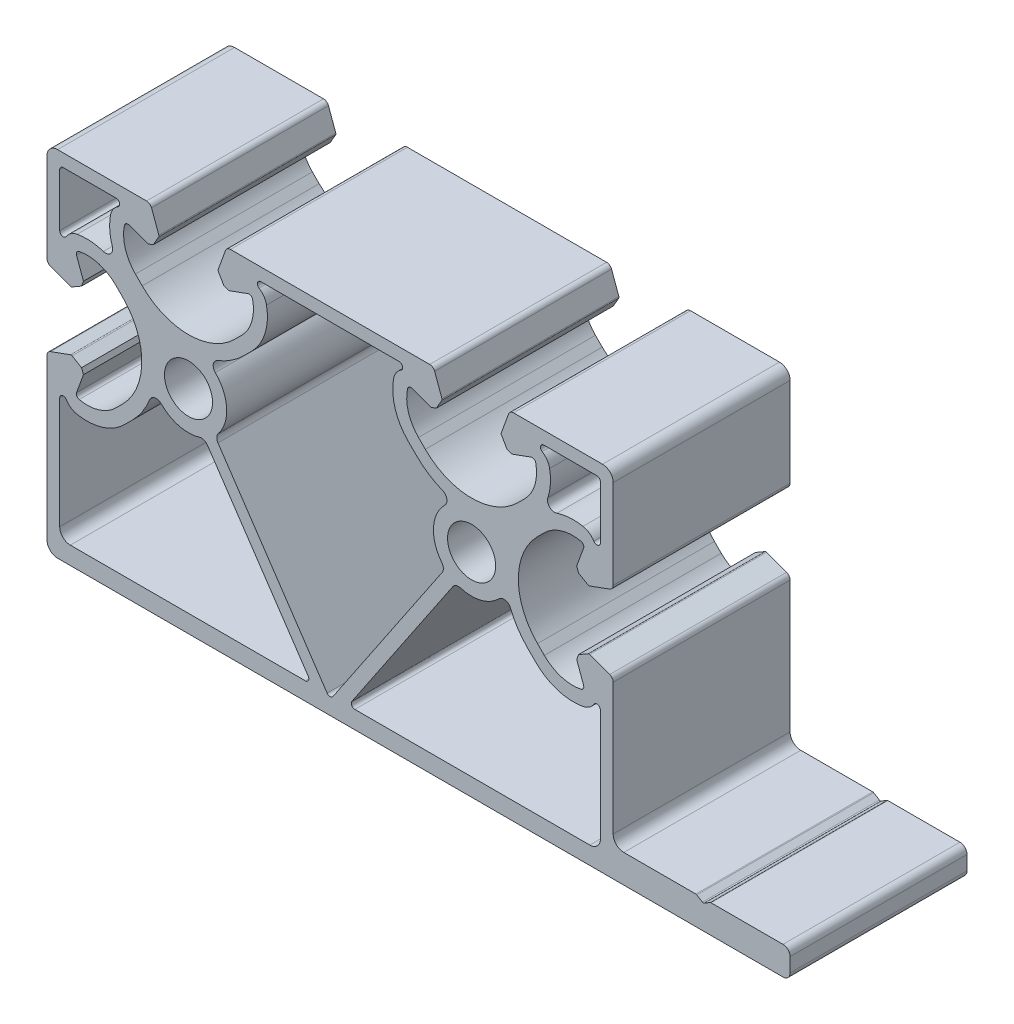
SolidWorks part; units mm, degrees
material "6005-T5"
ref_plane "Front" through (0, 0, 0) normal (0, 0, 1) x (1, 0, 0)
ref_plane "Top" through (0, 0, 0) normal (0, 1, 0) x (1, 0, 0)
ref_plane "Right" through (0, 0, 0) normal (1, 0, 0) x (0, 0, -1)
sketch "Sk Main Extrusion" plane through (0, 0, 0) normal (0, 0, 1) x (1, 0, 0)
  line L78 (-11.0507, 39.0722) -> (-12.1865, 37.9365)
  line L79 (-15.8391, 25.4341) -> (-0.4147, 2.5366)
  line L80 (0.4147, 2.5366) -> (15.8391, 25.4341)
  line L81 (12.1865, 37.9365) -> (11.0507, 39.0722)
  line L82 (9.7655, 48.2) -> (-9.7655, 48.2)
  line L83 (-27.9365, 22.1865) -> (-29.0722, 21.0507)
  line L84 (-38.2, 19.7655) -> (-38.2, 4)
  line L85 (-36.7, 2.5) -> (-3.5, 2.5)
  line L86 (-3.0853, 3.2793) -> (-17.332, 24.4285)
  line L87 (-38.2, 47.7) -> (-38.2, 40.2345)
  line L88 (-30.2345, 48.2) -> (-37.7, 48.2)
  line L89 (17.332, 24.4285) -> (3.0853, 3.2793)
  line L90 (3.5, 2.5) -> (36.7, 2.5)
  line L91 (38.2, 4) -> (38.2, 19.7655)
  line L92 (29.0722, 21.0507) -> (27.9365, 22.1865)
  line L93 (38.2, 40.2345) -> (38.2, 47.7)
  line L94 (37.7, 48.2) -> (30.2345, 48.2)
  line L95 (-36.6712, 25.8099) -> (-39.5065, 24.7779)
  line L96 (-40, 24.0732) -> (-40, 1.5)
  line L97 (-38.5, 0) -> (64, 0)
  line L98 (65, 1) -> (65, 3)
  line L99 (64, 4) -> (53.8207, 4)
  line L100 (53.6919, 3.9643) -> (52.8788, 3.4757)
  line L101 (52.6212, 3.4757) -> (51.8081, 3.9643)
  line L102 (51.6793, 4) -> (41.5, 4)
  line L103 (40, 5.5) -> (40, 24.0732)
  line L104 (39.5065, 24.7779) -> (36.6712, 25.8099)
  line L105 (36.4607, 25.7915) -> (35.1113, 25.0124)
  line L106 (35.1113, 25.0124) -> (34.8453, 24.2815)
  line L107 (34.8453, 24.2815) -> (35.8198, 21.6038)
  line L108 (30.2727, 22.4958) -> (29.3093, 23.4593)
  line L109 (29.3093, 36.5407) -> (30.2727, 37.5042)
  line L110 (35.8198, 38.3962) -> (34.8453, 35.7185)
  line L111 (34.8453, 35.7185) -> (35.1113, 34.9876)
  line L112 (35.1113, 34.9876) -> (36.4607, 34.2085)
  line L113 (36.6712, 34.1901) -> (39.5065, 35.2221)
  line L114 (40, 35.9268) -> (40, 48.5)
  line L115 (38.5, 50) -> (25.9268, 50)
  line L116 (25.2221, 49.5065) -> (24.1901, 46.6712)
  line L117 (24.2085, 46.4607) -> (24.9876, 45.1113)
  line L118 (24.9876, 45.1113) -> (25.7185, 44.8453)
  line L119 (25.7185, 44.8453) -> (28.3962, 45.8198)
  line L120 (27.5042, 40.2727) -> (26.5407, 39.3093)
  line L121 (13.4593, 39.3093) -> (12.4958, 40.2727)
  line L122 (11.6038, 45.8198) -> (14.2815, 44.8453)
  line L123 (14.2815, 44.8453) -> (15.0124, 45.1113)
  line L124 (15.0124, 45.1113) -> (15.7915, 46.4607)
  line L125 (15.8099, 46.6712) -> (14.7779, 49.5065)
  line L126 (14.0732, 50) -> (-14.0732, 50)
  line L127 (-14.7779, 49.5065) -> (-15.8099, 46.6712)
  line L128 (-15.7915, 46.4607) -> (-15.0124, 45.1113)
  line L129 (-15.0124, 45.1113) -> (-14.2815, 44.8453)
  line L130 (-14.2815, 44.8453) -> (-11.6038, 45.8198)
  line L131 (-12.4958, 40.2727) -> (-13.4593, 39.3093)
  line L132 (-26.5407, 39.3093) -> (-27.5042, 40.2727)
  line L133 (-28.3962, 45.8198) -> (-25.7185, 44.8453)
  line L134 (-25.7185, 44.8453) -> (-24.9876, 45.1113)
  line L135 (-24.9876, 45.1113) -> (-24.2085, 46.4607)
  line L136 (-24.1901, 46.6712) -> (-25.2221, 49.5065)
  line L137 (-25.9268, 50) -> (-38.5, 50)
  line L138 (-40, 48.5) -> (-40, 35.9268)
  line L139 (-39.5065, 35.2221) -> (-36.6712, 34.1901)
  line L140 (-36.4607, 34.2085) -> (-35.1113, 34.9876)
  line L141 (-35.1113, 34.9876) -> (-34.8453, 35.7185)
  line L142 (-34.8453, 35.7185) -> (-35.8198, 38.3962)
  line L143 (-30.2727, 37.5042) -> (-29.3093, 36.5407)
  line L144 (-29.3093, 23.4593) -> (-30.2727, 22.4958)
  line L145 (-35.8198, 21.6038) -> (-34.8453, 24.2815)
  line L146 (-34.8453, 24.2815) -> (-35.1113, 25.0124)
  line L147 (-35.1113, 25.0124) -> (-36.4607, 25.7915)
  circle A96 centre (-20, 30) radius 3.4
  circle A97 centre (20, 30) radius 3.4
  arc A98 (-9.7655, 48.2) -> (-10.0289, 47.275) centre (-9.7655, 47.7) ccw
  arc A99 (-8.9787, 45.7377) -> (-10.0289, 47.275) centre (-11.2405, 45.32) ccw
  arc A100 (-11.0507, 39.0722) -> (-8.9787, 45.7377) centre (-16.354, 44.3755) ccw
  arc A101 (-15.8873, 35.4939) -> (-12.1865, 37.9365) centre (-20, 45.75) ccw
  arc A102 (-15.8873, 35.4939) -> (-16.2159, 33.8523) centre (-15.5151, 34.5657) ccw
  arc A103 (-15.7895, 26.6189) -> (-16.2159, 33.8523) centre (-20, 30) ccw
  arc A104 (-15.7895, 26.6189) -> (-15.8391, 25.4341) centre (-15.0098, 25.9928) ccw
  arc A105 (-0.4147, 2.5366) -> (0.4147, 2.5366) centre (0, 2.816) ccw
  arc A106 (15.8391, 25.4341) -> (15.7895, 26.6189) centre (15.0098, 25.9928) ccw
  arc A107 (16.2159, 33.8523) -> (15.7895, 26.6189) centre (20, 30) ccw
  arc A108 (16.2159, 33.8523) -> (15.8873, 35.4939) centre (15.5151, 34.5657) ccw
  arc A109 (12.1865, 37.9365) -> (15.8873, 35.4939) centre (20, 45.75) ccw
  arc A110 (8.9787, 45.7377) -> (11.0507, 39.0722) centre (16.354, 44.3755) ccw
  arc A111 (10.0289, 47.275) -> (8.9787, 45.7377) centre (11.2405, 45.32) ccw
  arc A112 (10.0289, 47.275) -> (9.7655, 48.2) centre (9.7655, 47.7) ccw
  arc A113 (-23.8523, 26.2159) -> (-25.4939, 25.8873) centre (-24.5657, 25.5151) ccw
  arc A114 (-27.9365, 22.1865) -> (-25.4939, 25.8873) centre (-35.75, 30) ccw
  arc A115 (-39.5065, 24.7779) -> (-40, 24.0732) centre (-39.25, 24.0732) ccw
  arc A116 (-40, 1.5) -> (-38.5, 0) centre (-38.5, 1.5) ccw
  arc A117 (64, 0) -> (65, 1) centre (64, 1) ccw
  arc A118 (65, 3) -> (64, 4) centre (64, 3) ccw
  arc A119 (53.8207, 4) -> (53.6919, 3.9643) centre (53.8207, 3.75) ccw
  arc A120 (52.6212, 3.4757) -> (52.8788, 3.4757) centre (52.75, 3.69) ccw
  arc A121 (51.8081, 3.9643) -> (51.6793, 4) centre (51.6793, 3.75) ccw
  arc A122 (40, 5.5) -> (41.5, 4) centre (41.5, 5.5) ccw
  arc A123 (40, 24.0732) -> (39.5065, 24.7779) centre (39.25, 24.0732) ccw
  arc A124 (36.6712, 25.8099) -> (36.4607, 25.7915) centre (36.5857, 25.575) ccw
  arc A125 (35.4507, 20.943) -> (35.8198, 21.6038) centre (35.35, 21.4328) ccw
  arc A126 (30.2727, 22.4958) -> (35.4507, 20.943) centre (34.3032, 26.5263) ccw
  arc A127 (29.3093, 36.5407) -> (29.3093, 23.4593) centre (35.85, 30) ccw
  arc A128 (35.4507, 39.057) -> (30.2727, 37.5042) centre (34.3032, 33.4737) ccw
  arc A129 (35.8198, 38.3962) -> (35.4507, 39.057) centre (35.35, 38.5672) ccw
  arc A130 (36.4607, 34.2085) -> (36.6712, 34.1901) centre (36.5857, 34.425) ccw
  arc A131 (39.5065, 35.2221) -> (40, 35.9268) centre (39.25, 35.9268) ccw
  arc A132 (40, 48.5) -> (38.5, 50) centre (38.5, 48.5) ccw
  arc A133 (25.9268, 50) -> (25.2221, 49.5065) centre (25.9268, 49.25) ccw
  arc A134 (24.1901, 46.6712) -> (24.2085, 46.4607) centre (24.425, 46.5857) ccw
  arc A135 (29.057, 45.4507) -> (28.3962, 45.8198) centre (28.5672, 45.35) ccw
  arc A136 (27.5042, 40.2727) -> (29.057, 45.4507) centre (23.4737, 44.3032) ccw
  arc A137 (13.4593, 39.3093) -> (26.5407, 39.3093) centre (20, 45.85) ccw
  arc A138 (10.943, 45.4507) -> (12.4958, 40.2727) centre (16.5263, 44.3032) ccw
  arc A139 (11.6038, 45.8198) -> (10.943, 45.4507) centre (11.4328, 45.35) ccw
  arc A140 (15.7915, 46.4607) -> (15.8099, 46.6712) centre (15.575, 46.5857) ccw
  arc A141 (14.7779, 49.5065) -> (14.0732, 50) centre (14.0732, 49.25) ccw
  arc A142 (-14.0732, 50) -> (-14.7779, 49.5065) centre (-14.0732, 49.25) ccw
  arc A143 (-15.8099, 46.6712) -> (-15.7915, 46.4607) centre (-15.575, 46.5857) ccw
  arc A144 (-10.943, 45.4507) -> (-11.6038, 45.8198) centre (-11.4328, 45.35) ccw
  arc A145 (-12.4958, 40.2727) -> (-10.943, 45.4507) centre (-16.5263, 44.3032) ccw
  arc A146 (-26.5407, 39.3093) -> (-13.4593, 39.3093) centre (-20, 45.85) ccw
  arc A147 (-29.057, 45.4507) -> (-27.5042, 40.2727) centre (-23.4737, 44.3032) ccw
  arc A148 (-28.3962, 45.8198) -> (-29.057, 45.4507) centre (-28.5672, 45.35) ccw
  arc A149 (-24.2085, 46.4607) -> (-24.1901, 46.6712) centre (-24.425, 46.5857) ccw
  arc A150 (-25.2221, 49.5065) -> (-25.9268, 50) centre (-25.9268, 49.25) ccw
  arc A151 (-38.5, 50) -> (-40, 48.5) centre (-38.5, 48.5) ccw
  arc A152 (-40, 35.9268) -> (-39.5065, 35.2221) centre (-39.25, 35.9268) ccw
  arc A153 (-36.6712, 34.1901) -> (-36.4607, 34.2085) centre (-36.5857, 34.425) ccw
  arc A154 (-35.4507, 39.057) -> (-35.8198, 38.3962) centre (-35.35, 38.5672) ccw
  arc A155 (-30.2727, 37.5042) -> (-35.4507, 39.057) centre (-34.3032, 33.4737) ccw
  arc A156 (-29.3093, 23.4593) -> (-29.3093, 36.5407) centre (-35.85, 30) ccw
  arc A157 (-35.4507, 20.943) -> (-30.2727, 22.4958) centre (-34.3032, 26.5263) ccw
  arc A158 (-35.8198, 21.6038) -> (-35.4507, 20.943) centre (-35.35, 21.4328) ccw
  arc A159 (-36.4607, 25.7915) -> (-36.6712, 25.8099) centre (-36.5857, 25.575) ccw
  arc A160 (-35.7377, 18.9787) -> (-29.0722, 21.0507) centre (-34.3755, 26.354) ccw
  arc A161 (-37.275, 20.0289) -> (-35.7377, 18.9787) centre (-35.32, 21.2405) ccw
  arc A162 (-37.275, 20.0289) -> (-38.2, 19.7655) centre (-37.7, 19.7655) ccw
  arc A163 (-38.2, 4) -> (-36.7, 2.5) centre (-36.7, 4) ccw
  arc A164 (-3.5, 2.5) -> (-3.0853, 3.2793) centre (-3.5, 3) ccw
  arc A165 (-17.332, 24.4285) -> (-18.4487, 24.8276) centre (-18.1614, 23.8698) ccw
  arc A166 (-23.8523, 26.2159) -> (-18.4487, 24.8276) centre (-20, 30) ccw
  arc A167 (-37.7, 48.2) -> (-38.2, 47.7) centre (-37.7, 47.7) ccw
  arc A168 (-38.2, 40.2345) -> (-37.275, 39.9711) centre (-37.7, 40.2345) ccw
  arc A169 (-35.7377, 41.0213) -> (-37.275, 39.9711) centre (-35.32, 38.7595) ccw
  arc A170 (-32.0331, 40.7708) -> (-35.7377, 41.0213) centre (-34.3755, 33.646) ccw
  arc A171 (-32.0331, 40.7708) -> (-30.7708, 42.0331) centre (-31.7208, 41.7208) ccw
  arc A172 (-31.0213, 45.7377) -> (-30.7708, 42.0331) centre (-23.646, 44.3755) ccw
  arc A173 (-29.9711, 47.275) -> (-31.0213, 45.7377) centre (-28.7595, 45.32) ccw
  arc A174 (-29.9711, 47.275) -> (-30.2345, 48.2) centre (-30.2345, 47.7) ccw
  arc A175 (18.4487, 24.8276) -> (17.332, 24.4285) centre (18.1614, 23.8698) ccw
  arc A176 (3.0853, 3.2793) -> (3.5, 2.5) centre (3.5, 3) ccw
  arc A177 (36.7, 2.5) -> (38.2, 4) centre (36.7, 4) ccw
  arc A178 (38.2, 19.7655) -> (37.275, 20.0289) centre (37.7, 19.7655) ccw
  arc A179 (35.7377, 18.9787) -> (37.275, 20.0289) centre (35.32, 21.2405) ccw
  arc A180 (29.0722, 21.0507) -> (35.7377, 18.9787) centre (34.3755, 26.354) ccw
  arc A181 (25.4939, 25.8873) -> (27.9365, 22.1865) centre (35.75, 30) ccw
  arc A182 (25.4939, 25.8873) -> (23.8523, 26.2159) centre (24.5657, 25.5151) ccw
  arc A183 (18.4487, 24.8276) -> (23.8523, 26.2159) centre (20, 30) ccw
  arc A184 (30.2345, 48.2) -> (29.9711, 47.275) centre (30.2345, 47.7) ccw
  arc A185 (31.0213, 45.7377) -> (29.9711, 47.275) centre (28.7595, 45.32) ccw
  arc A186 (30.7708, 42.0331) -> (31.0213, 45.7377) centre (23.646, 44.3755) ccw
  arc A187 (30.7708, 42.0331) -> (32.0331, 40.7708) centre (31.7208, 41.7208) ccw
  arc A188 (35.7377, 41.0213) -> (32.0331, 40.7708) centre (34.3755, 33.646) ccw
  arc A189 (37.275, 39.9711) -> (35.7377, 41.0213) centre (35.32, 38.7595) ccw
  arc A190 (37.275, 39.9711) -> (38.2, 40.2345) centre (37.7, 40.2345) ccw
  arc A191 (38.2, 47.7) -> (37.7, 48.2) centre (37.7, 47.7) ccw
  point P238 (0, 25)
extrude "Main Extrusion" add sketch "Sk Main Extrusion" against normal blind 25
sketch "Threaded Insert Mate Sketch" plane through (0, 0, 0) normal (0, 0, 1) x (1, 0, 0)
  line L0 (-32.7, 30) -> (-20, 30) construction
  line L1 (0, 0) -> (0, 50) construction
  line L3 (14.0732, 50) -> (-14.0732, 50) construction
  circle A1 centre (-32.7, 30) radius 5.65
  circle A3 centre (-20, 42.7) radius 5.65
  circle A4 centre (-7.3, 30) radius 5.65
  circle A5 centre (-20, 17.3) radius 5.65
  circle A6 centre (32.7, 30) radius 5.65
  circle A7 centre (20, 42.7) radius 5.65
  circle A8 centre (-20, 30) radius 3.4 construction
  point P3 (0, 0)
  point P5 (0, 0)
  point P6 (-20.5567, 29.9016)
  point P21 (-20, 30)
  point P23 (0, 0)
  point P24 (0, 0)
  dimension "D2" = 12.7
  dimension "D4" = 11.3
  dimension "D1" = 4
equation "\"Weight kg\"= round ( \"SW-Mass\" , 2 )"
equation "\"Weight lbs\"= round ( \"SW-Mass\" * 2.2046 , 2 )"
equation "\"Length mm\"= round ( \"Length@Main Extrusion\" , 2 )"
equation "\"Length in\"= round ( \"Length@Main Extrusion\" / 25.4 , 3 )"
